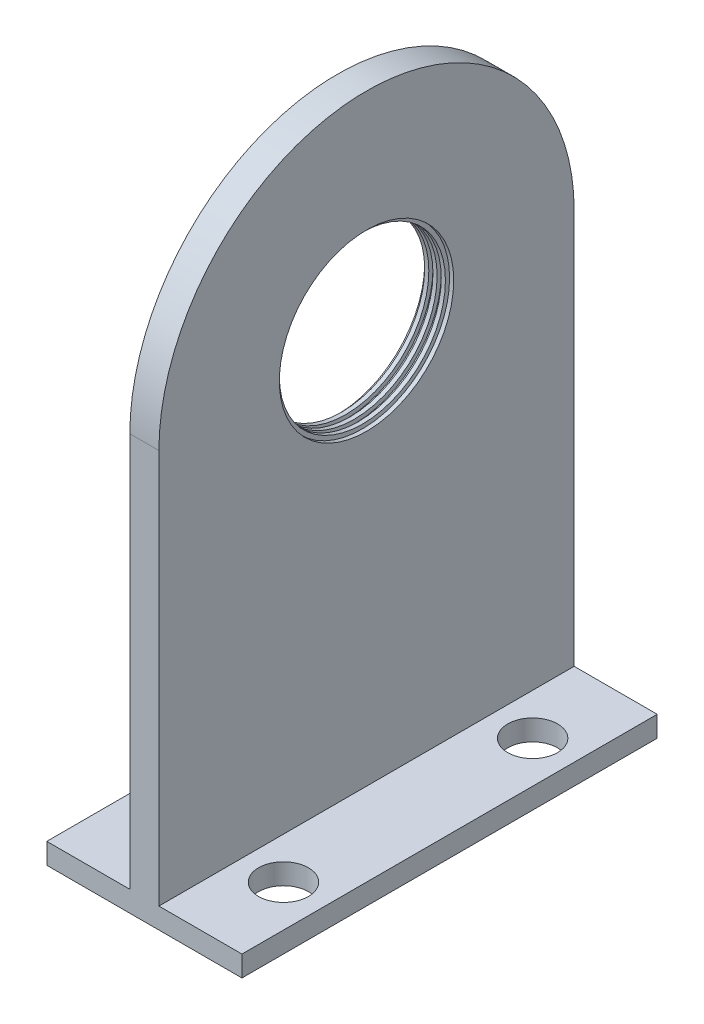
SolidWorks part; units mm, degrees
material "1023 Carbon Steel Sheet (SS)"
ref_plane "Front" through (0, 0, 0) normal (0, 0, 1) x (1, 0, 0)
ref_plane "Top" through (0, 0, 0) normal (0, 1, 0) x (1, 0, 0)
ref_plane "Right" through (0, 0, 0) normal (1, 0, 0) x (0, 0, -1)
sketch "Sketch1" plane through (0, 0, 0) normal (1, 0, 0) x (0, 0, -1)
  line L0 (0, 55) -> (0, -55) construction
  line L1 (-5, 0) -> (5, 0)
  line L2 (-5, 0) -> (-5, 10)
  line L4 (5, 0) -> (5, 10)
  line L5 (55, 0) -> (-55, 0) construction
  arc A0 (-5, 10) -> (5, 10) centre (0, 10) cw
  circle A1 centre (0, 10) radius 2
  dimension "D4" = 5
  dimension "D5" = 4
  dimension "D1" = 10
  dimension "D2" = 5
  dimension "D3" = 10
extrude "Boss-Extrude1" add sketch "Sketch1" along normal blind 0.7
ref_plane "Plane1" through (0.1, 0, 0) normal (1, 0, 0) x (0, 0, -1)
ref_plane "Plane2" through (0.3, 0, 0) normal (1, 0, 0) x (0, 0, -1)
ref_plane "Plane3" through (0.5, 0, 0) normal (1, 0, 0) x (0, 0, -1)
ref_plane "Plane4" through (0.7, 0, 0) normal (1, 0, 0) x (0, 0, -1)
sketch "Sketch2" plane through (0, 0, 0) normal (1, 0, 0) x (0, 0, -1)
  circle A0 centre (0, 10) radius 2.1
extrude "Cut-Extrude1" cut sketch "Sketch2" along normal blind 0.1
sketch "Sketch3" plane through (0.7, 0, 0) normal (1, 0, 0) x (0, 0, -1)
  circle A0 centre (0, 10) radius 2.1
  dimension "D1" = 4.2
extrude "Cut-Extrude2" cut sketch "Sketch3" against normal blind 0.1
sketch "Sketch4" plane through (0.5, 0, 0) normal (1, 0, 0) x (0, 0, -1)
  circle A0 centre (0, 10) radius 2.1
extrude "Cut-Extrude3" cut sketch "Sketch4" against normal blind 0.1
sketch "Sketch5" plane through (0.3, 0, 0) normal (1, 0, 0) x (0, 0, -1)
  circle A0 centre (0, 10) radius 2.1
extrude "Cut-Extrude4" cut sketch "Sketch5" against normal blind 0.1
sketch "Sketch6" plane through (0, 0, 0) normal (1, 0, 0) x (0, 0, -1)
  line L1 (-5, 0) -> (5, 0)
  line L2 (-5, 0) -> (-5, 0.5)
  line L3 (-5, 0.5) -> (5, 0.5)
  line L4 (5, 0) -> (5, 0.5)
  dimension "D1" = 0.5
extrude "Boss-Extrude2" add sketch "Sketch6" along normal blind 2.7 and the other way blind 2
sketch "Sketch7" plane through (0, 0.5, 0) normal (0, 1, 0) x (1, 0, 0)
  line L0 (2.7, 5) -> (2.7, -5) construction
  line L3 (-2.585, 0) -> (2.585, 0) construction
  circle A0 centre (1.7, 3) radius 0.6
  circle A1 centre (1.7, -3) radius 0.6
  dimension "D1" = 1.2
  dimension "D2" = 1.2
  dimension "D3" = 1
  dimension "D4" = 1
  dimension "D5" = 3
  dimension "D6" = 3
extrude "Cut-Extrude5" cut sketch "Sketch7" against normal blind 2.7
sketch "Sketch8" plane through (0, 0.5, 0) normal (0, 1, 0) x (1, 0, 0)
  line L1 (-2, 5) -> (-2, -5) construction
  line L2 (-2.585, 0) -> (2.585, 0) construction
  circle A0 centre (-1, 3) radius 0.6
  circle A1 centre (-1, -3) radius 0.6
  dimension "D1" = 1.2
  dimension "D2" = 1.2
  dimension "D3" = 1
  dimension "D4" = 1
  dimension "D5" = 3
  dimension "D6" = 3
extrude "Cut-Extrude6" cut sketch "Sketch8" against normal blind 2.7
